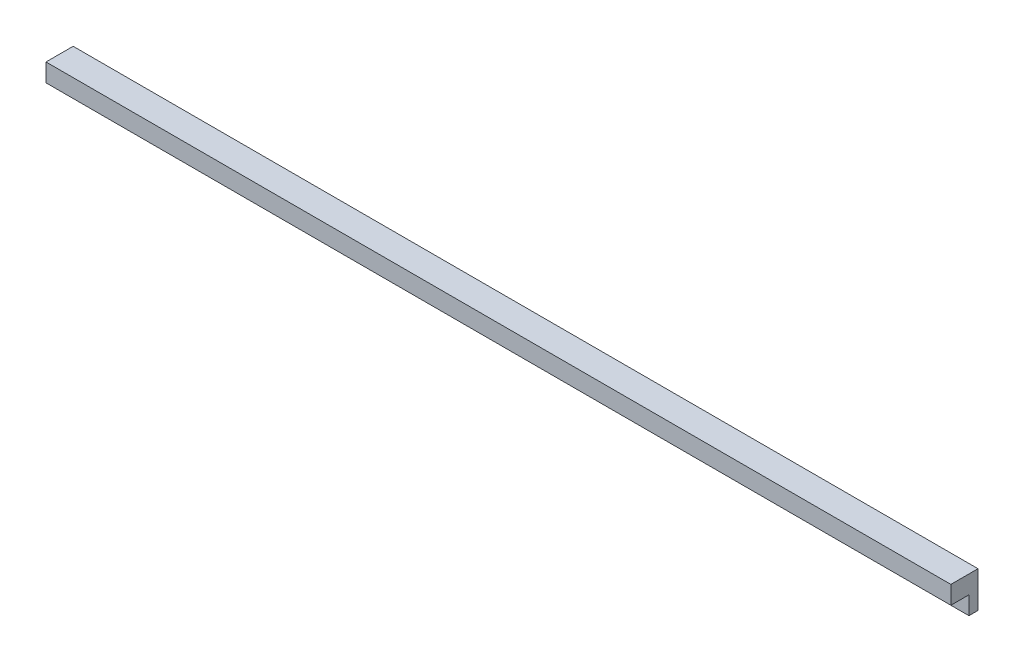
SolidWorks part; units mm, degrees
ref_plane "Front Plane" through (0, 0, 0) normal (0, 0, 1) x (1, 0, 0)
ref_plane "Top Plane" through (0, 0, 0) normal (0, 1, 0) x (1, 0, 0)
ref_plane "Right Plane" through (0, 0, 0) normal (1, 0, 0) x (0, 0, -1)
sketch "Sketch2" plane through (0, 0, 0) normal (0, 1, 0) x (1, 0, 0)
  line L1 (250, -7.5) -> (-250, -7.5)
  line L2 (250, -7.5) -> (250, 7.5)
  line L3 (250, 7.5) -> (-250, 7.5)
  line L4 (-250, -7.5) -> (-250, 7.5)
  line L5 (250, -7.5) -> (-250, 7.5) construction
  line L6 (250, 7.5) -> (-250, -7.5) construction
  point P0 (0, 0)
extrude "Boss-Extrude3" add sketch "Sketch2" along normal blind 10
sketch "Sketch5" plane through (0, 0, 0) normal (0, 1, 0) x (1, 0, 0)
  line L0 (250, -7.5) -> (250, 7.5) construction
  line L1 (-250, 7.5) -> (250, 7.5)
  line L2 (-250, 7.5) -> (-250, 2.5)
  line L3 (-250, 2.5) -> (250, 2.5)
  line L4 (250, 7.5) -> (250, 2.5)
extrude "Boss-Extrude5" add sketch "Sketch5" against normal blind 10
